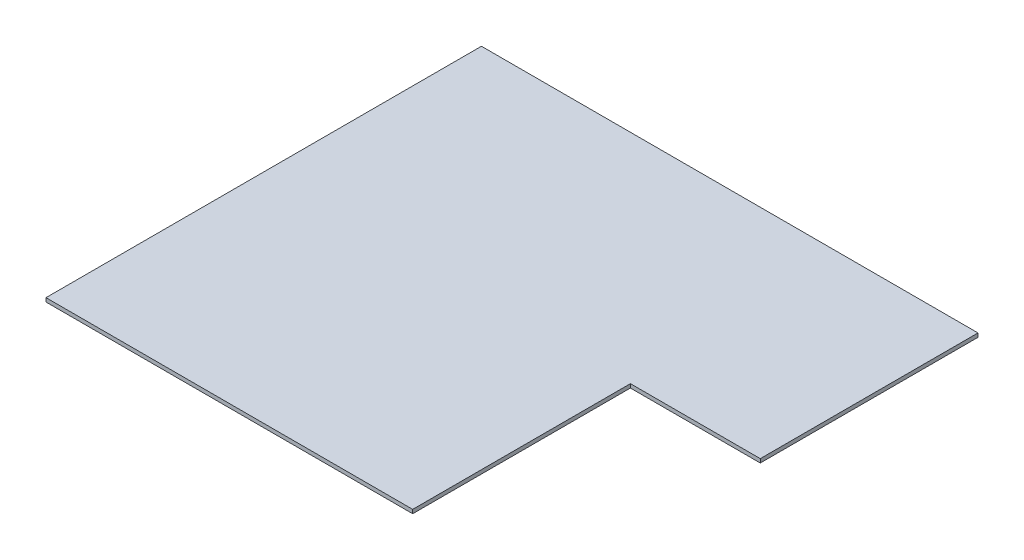
SolidWorks part; units mm, degrees
ref_plane "Front" through (0, 0, 0) normal (0, 0, 1) x (1, 0, 0)
ref_plane "Top" through (0, 0, 0) normal (0, 1, 0) x (1, 0, 0)
ref_plane "Right" through (0, 0, 0) normal (1, 0, 0) x (0, 0, -1)
sketch "Sketch1" plane through (0, 0, 0) normal (0, 1, 0) x (1, 0, 0)
  line L0 (0, 0) -> (0, 1447.8)
  line L1 (0, 1447.8) -> (1651, 1447.8)
  line L2 (1651, 1447.8) -> (1651, 723.9)
  line L3 (1651, 723.9) -> (1219.2, 723.9)
  line L4 (1219.2, 723.9) -> (1219.2, 0)
  line L5 (1219.2, 0) -> (0, 0)
  dimension "D1" = 1651
  dimension "D2" = 1447.8
  dimension "D3" = 431.8
  dimension "D4" = 723.9
extrude "Boss-Extrude1" add sketch "Sketch1" along normal blind 12.7
